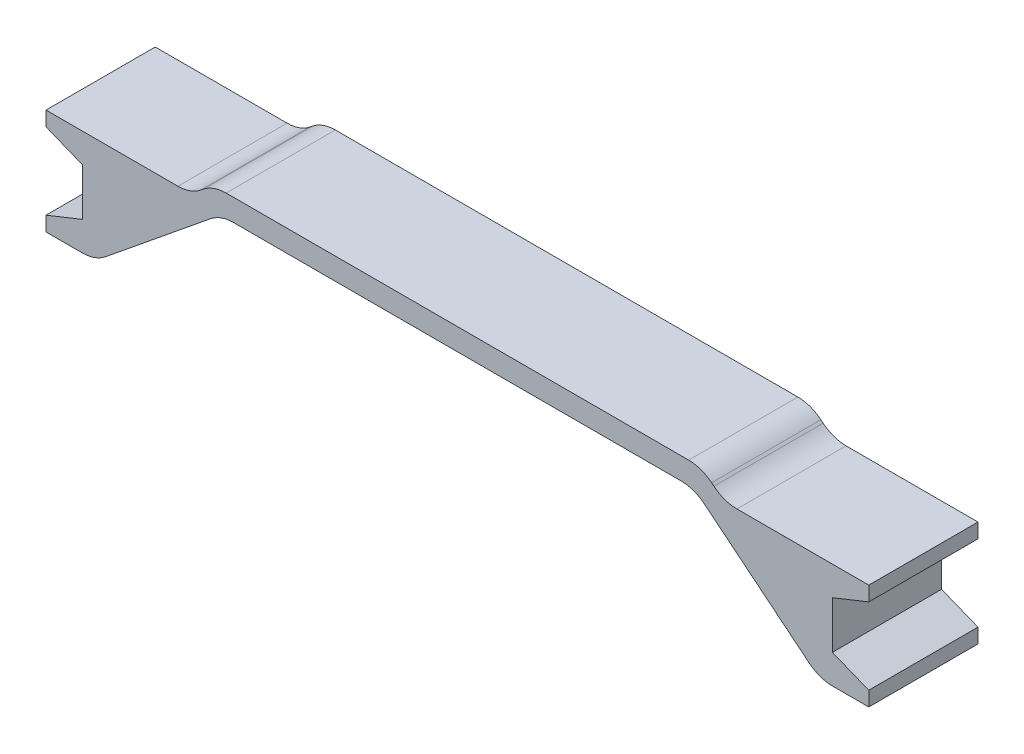
SolidWorks part; units mm, degrees
ref_plane "Front Plane" through (0, 0, 0) normal (0, 0, 1) x (1, 0, 0)
ref_plane "Top Plane" through (0, 0, 0) normal (0, 1, 0) x (1, 0, 0)
ref_plane "Right Plane" through (0, 0, 0) normal (1, 0, 0) x (0, 0, -1)
sketch "Sketch1" plane through (0, 0, 0) normal (0, 0, 1) x (1, 0, 0)
  line L0 (30.7396, -3) -> (-30.7396, -3)
  line L1 (-33.8953, -4.1216) -> (-48.3443, -15.8784)
  line L2 (-51.5, -17) -> (-56.5, -17)
  line L3 (-56.5, -17) -> (-56.5, -15)
  line L4 (-56.5, -15) -> (-51.5, -13)
  line L5 (-51.5, -13) -> (-51.5, -6.5)
  line L6 (-51.5, -6.5) -> (-56.5, -4.5)
  line L7 (-56.5, -4.5) -> (-56.5, -2.5)
  line L8 (-56.5, -2.5) -> (-38.3879, -2.5)
  line L9 (-35.2322, -1.3784) -> (-34.9167, -1.1216)
  line L10 (-31.761, 0) -> (31.761, 0)
  line L11 (-30.7817, 2.2429) -> (-28.5872, 0.1974) construction
  line L12 (0, -3) -> (0, 0) construction
  line L13 (35.2322, -1.3784) -> (34.9167, -1.1216)
  line L14 (56.5, -2.5) -> (38.3879, -2.5)
  line L15 (56.5, -4.5) -> (56.5, -2.5)
  line L16 (51.5, -6.5) -> (56.5, -4.5)
  line L17 (51.5, -13) -> (51.5, -6.5)
  line L18 (56.5, -15) -> (51.5, -13)
  line L19 (56.5, -17) -> (56.5, -15)
  line L20 (51.5, -17) -> (56.5, -17)
  line L21 (33.8953, -4.1216) -> (48.3443, -15.8784)
  arc A0 (-48.3443, -15.8784) -> (-51.5, -17) centre (-51.5, -12) cw
  arc A1 (-30.7396, -3) -> (-33.8953, -4.1216) centre (-30.7396, -8) ccw
  arc A2 (-34.9167, -1.1216) -> (-31.761, 0) centre (-31.761, -5) cw
  arc A3 (-38.3879, -2.5) -> (-35.2322, -1.3784) centre (-38.3879, 2.5) ccw
  arc A4 (38.3879, -2.5) -> (35.2322, -1.3784) centre (38.3879, 2.5) cw
  arc A5 (34.9167, -1.1216) -> (31.761, 0) centre (31.761, -5) ccw
  arc A6 (30.7396, -3) -> (33.8953, -4.1216) centre (30.7396, -8) cw
  arc A7 (48.3443, -15.8784) -> (51.5, -17) centre (51.5, -12) ccw
  point P13 (0, -3)
  point P30 (0, 0)
  dimension "D2" = 5
  dimension "D1" = 6.5
  dimension "D3" = 3
  dimension "D4" = 2
  dimension "D5" = 5
  dimension "D6" = 17
  dimension "D7" = 2
  dimension "D8" = 103
  dimension "D9" = 5
extrude "Boss-Extrude1" add sketch "Sketch1" along normal blind 15
